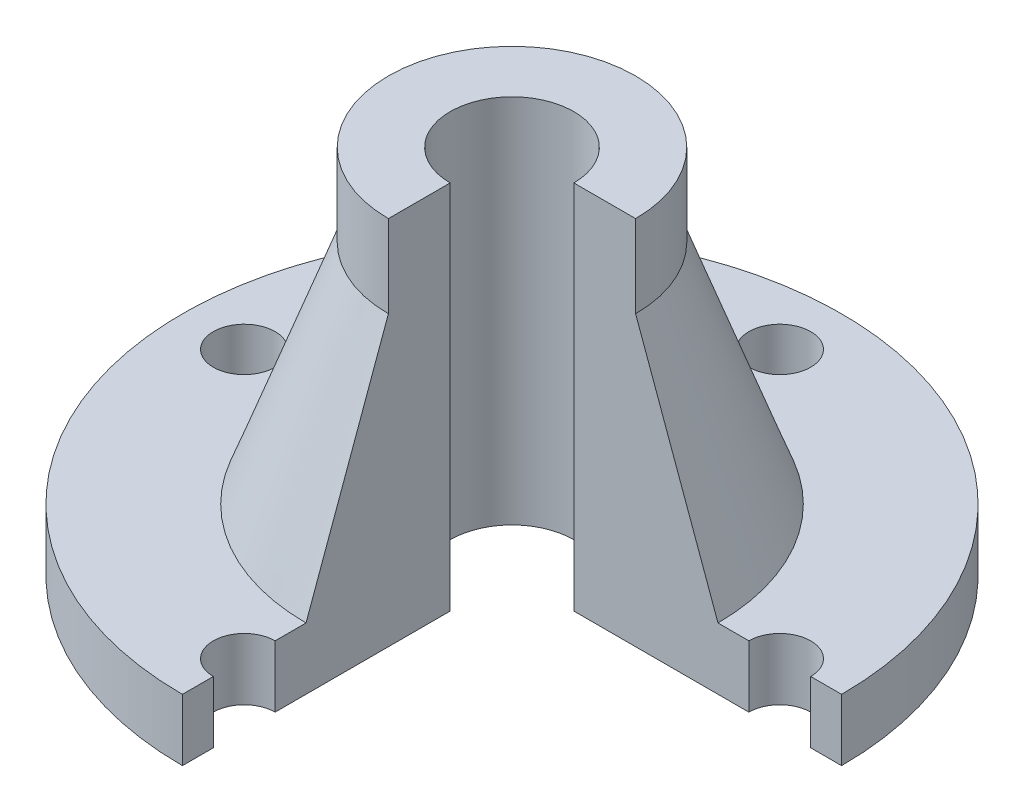
SolidWorks part; units mm, degrees
ref_plane "Front Plane" through (0, 0, 0) normal (0, 0, 1) x (1, 0, 0)
ref_plane "Top Plane" through (0, 0, 0) normal (0, 1, 0) x (1, 0, 0)
ref_plane "Right Plane" through (0, 0, 0) normal (1, 0, 0) x (0, 0, -1)
sketch "Sketch1" plane through (0, 0, 0) normal (0, 1, 0) x (1, 0, 0)
  circle A0 centre (0, 0) radius 80
  dimension "D1" = 160
extrude "Boss-Extrude1" add sketch "Sketch1" along normal blind 15
sketch "Sketch2" plane through (0, 15, 0) normal (0, 1, 0) x (1, 0, 0)
  circle A0 centre (0, 0) radius 50
extrude "Boss-Extrude2" add sketch "Sketch2" along normal blind 75
sketch "Sketch3" plane through (0, 0, 0) normal (0, 1, 0) x (1, 0, 0)
  circle A0 centre (0, 0) radius 30
  circle A1 centre (0, 0) radius 15
extrude "Cut-Extrude1" cut sketch "Sketch3" along normal through all contours A1
sketch "Sketch4" plane through (0, 0, 0) normal (1, 0, 0) x (0, 0, -1)
  line L0 (-50, 90) -> (-30, 90) construction
  line L1 (0, 90) -> (0, 15) construction
  line L2 (-30, 90) -> (-30, 70)
  line L3 (-30, 70) -> (-50, 15)
  line L4 (80, 15) -> (-80, 15) construction
  line L5 (-50, 15) -> (-50, 90)
  line L6 (-50, 90) -> (-30, 90)
  line L7 (15, 90) -> (-15, 90) construction
  point P7 (0, 90)
revolve "Cut-Revolve1" cut sketch "Sketch4" angle 360 about L1
sketch "Sketch5" plane through (0, 0, 0) normal (0, -1, 0) x (1, 0, 0)
  circle A0 centre (0, 0) radius 65
  circle A1 centre (0, -65) radius 7.5
  dimension "D1" = 130
  dimension "D2" = 15
extrude "Cut-Extrude2" cut sketch "Sketch5" against normal blind 75 contours A0 A1 | A0 A1
pattern_circular "CirPattern1" count 4 over 360 about axis through (0, 0, 0) along (0, 1, 0) of "Cut-Extrude2"
sketch "Sketch6" plane through (0, 0, 0) normal (0, -1, 0) x (1, 0, 0)
  line L0 (0, 80) -> (0, 0)
  line L1 (0, 0) -> (80, 0)
  line L2 (80, 0) -> (80, 86.2107)
  line L3 (80, 86.2107) -> (0, 80)
  circle A0 centre (0, 0) radius 80 construction
extrude "Cut-Extrude3" cut sketch "Sketch6" against normal through all
